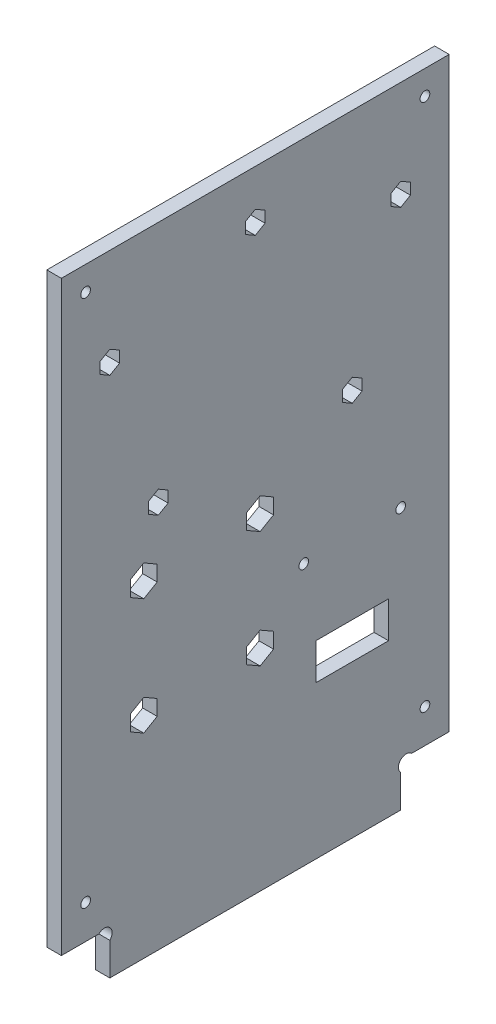
SolidWorks part; units mm, degrees
ref_plane "Plan de face" through (0, 0, 0) normal (0, 0, 1) x (1, 0, 0)
ref_plane "Plan de dessus" through (0, 0, 0) normal (0, 1, 0) x (1, 0, 0)
ref_plane "Plan de droite" through (0, 0, 0) normal (1, 0, 0) x (0, 0, -1)
sketch "Esquisse1" plane through (0, 0, 0) normal (1, 0, 0) x (0, 0, -1)
  line L8 (10, 6.7373) -> (10, 0)
  line L9 (70, 6.7373) -> (70, 0)
  line L10 (7.7373, 9) -> (0, 9)
  line L11 (10, 0) -> (70, 0)
  line L12 (72.2627, 9) -> (80, 9)
  line L13 (0, 9) -> (0, 130)
  line L14 (0, 130) -> (80, 130)
  line L15 (80, 130) -> (80, 9)
  arc A0 (10, 6.7373) -> (7.7373, 9) centre (8.8686, 7.8686) ccw
  arc A1 (70, 6.7373) -> (72.2627, 9) centre (71.1314, 7.8686) cw
  dimension "D7" = 1.1314
  dimension "D6" = 1.6
  dimension "D1" = 9
  dimension "D2" = 10
  dimension "D3" = 10
  dimension "D4" = 80
  dimension "D5" = 130
  dimension "D8" = 1.1314
  dimension "D9" = 1.1314
  dimension "D10" = 1.1314
extrude "Extrusion1" add sketch "Esquisse1" along normal blind 3
sketch "Esquisse2" plane through (3, 0, 0) normal (1, 0, 0) x (0, 0, -1)
  line L0 (0, 9) -> (7.7373, 9) construction
  line L1 (0, 130) -> (0, 9) construction
  line L2 (80, 9) -> (80, 130) construction
  line L3 (72.2627, 9) -> (80, 9) construction
  line L4 (80, 130) -> (0, 130) construction
  circle A0 centre (60, 80) radius 1
  circle A1 centre (10, 110) radius 1
  circle A2 centre (20, 80) radius 1
  circle A3 centre (70, 110) radius 1
  circle A4 centre (17, 67.45) radius 1.5
  circle A5 centre (17, 43.45) radius 1.5
  circle A6 centre (41, 43.45) radius 1.5
  circle A7 centre (41, 67.45) radius 1.5
  circle A8 centre (40, 120) radius 1
  circle A9 centre (70, 54) radius 1
  circle A10 centre (50, 54) radius 1
  dimension "D5" = 17
  dimension "D7" = 10
  dimension "D9" = 10
  dimension "D4" = 3
  dimension "D6" = 2
  dimension "D1" = 58.45
  dimension "D2" = 24
  dimension "D3" = 24
  dimension "D8" = 40
  dimension "D10" = 30
  dimension "D11" = 10
  dimension "D12" = 20
  dimension "D13" = 10
  dimension "D14" = 10
  dimension "D15" = 10
  dimension "D16" = 20
  dimension "D17" = 45
extrude "Enlèv. mat.-Extru.1" cut sketch "Esquisse2" against normal through all
sketch "Esquisse3" plane through (0, 0, 0) normal (-1, 0, 0) x (0, 0, 1)
  line L1 (-67.5, 39) -> (-52.5, 39)
  line L2 (-67.5, 39) -> (-67.5, 31.5)
  line L3 (-67.5, 31.5) -> (-52.5, 31.5)
  line L4 (-52.5, 39) -> (-52.5, 31.5)
  circle A0 centre (-70, 54) radius 1 construction
  circle A1 centre (-50, 54) radius 1 construction
  dimension "D4" = 2.5
  dimension "D1" = 15
  dimension "D2" = 7.5
  dimension "D3" = 15
  dimension "D5" = 2.5
extrude "Enlèv. mat.-Extru.2" cut sketch "Esquisse3" against normal through all
sketch "Esquisse4" plane through (3, 0, 0) normal (1, 0, 0) x (0, 0, -1)
  line L0 (80, 130) -> (0, 130) construction
  line L1 (0, 130) -> (0, 9) construction
  line L2 (80, 9) -> (80, 130) construction
  line L3 (0, 9) -> (7.7373, 9) construction
  circle A0 centre (5, 125) radius 1
  circle A1 centre (75, 125) radius 1
  circle A2 centre (75, 16) radius 1
  circle A3 centre (5, 16) radius 1
  dimension "D1" = 2
  dimension "D2" = 5
  dimension "D3" = 5
  dimension "D4" = 5
  dimension "D5" = 7
extrude "Enlèv. mat.-Extru.3" cut sketch "Esquisse4" against normal through all
sketch "Esquisse5" plane through (3, 0, 0) normal (1, 0, 0) x (0, 0, -1)
  line L0 (0, 130) -> (0, 9) construction
  line L1 (12.0178, 111.165) -> (10, 112.33)
  line L2 (10, 112.33) -> (7.9822, 111.165)
  line L3 (7.9822, 111.165) -> (7.9822, 108.835)
  line L4 (7.9822, 108.835) -> (10, 107.67)
  line L5 (10, 107.67) -> (12.0178, 108.835)
  line L6 (12.0178, 108.835) -> (12.0178, 111.165)
  line L7 (0, 130) -> (0, 9) construction
  line L26 (42.0178, 118.835) -> (42.0178, 121.165)
  line L27 (42.0178, 121.165) -> (40, 122.33)
  line L28 (40, 122.33) -> (37.9822, 121.165)
  line L29 (37.9822, 121.165) -> (37.9822, 118.835)
  line L30 (37.9822, 118.835) -> (40, 117.67)
  line L31 (40, 117.67) -> (42.0178, 118.835)
  line L32 (70, 107.67) -> (72.0178, 108.835)
  line L33 (72.0178, 108.835) -> (72.0178, 111.165)
  line L34 (72.0178, 111.165) -> (70, 112.33)
  line L35 (70, 112.33) -> (67.9822, 111.165)
  line L36 (67.9822, 111.165) -> (67.9822, 108.835)
  line L37 (67.9822, 108.835) -> (70, 107.67)
  line L38 (62.0178, 78.835) -> (62.0178, 81.165)
  line L39 (62.0178, 81.165) -> (60, 82.33)
  line L40 (60, 82.33) -> (57.9822, 81.165)
  line L41 (57.9822, 81.165) -> (57.9822, 78.835)
  line L42 (57.9822, 78.835) -> (60, 77.67)
  line L43 (60, 77.67) -> (62.0178, 78.835)
  line L44 (22.0178, 78.835) -> (22.0178, 81.165)
  line L45 (22.0178, 81.165) -> (20, 82.33)
  line L46 (20, 82.33) -> (17.9822, 81.165)
  line L47 (17.9822, 81.165) -> (17.9822, 78.835)
  line L48 (17.9822, 78.835) -> (20, 77.67)
  line L49 (20, 77.67) -> (22.0178, 78.835)
  line L56 (43.7713, 65.85) -> (43.7713, 69.05)
  line L57 (43.7713, 69.05) -> (41, 70.65)
  line L58 (41, 70.65) -> (38.2287, 69.05)
  line L59 (38.2287, 69.05) -> (38.2287, 65.85)
  line L60 (38.2287, 65.85) -> (41, 64.25)
  line L61 (41, 64.25) -> (43.7713, 65.85)
  line L62 (43.7713, 41.85) -> (43.7713, 45.05)
  line L63 (43.7713, 45.05) -> (41, 46.65)
  line L64 (41, 46.65) -> (38.2287, 45.05)
  line L65 (38.2287, 45.05) -> (38.2287, 41.85)
  line L66 (38.2287, 41.85) -> (41, 40.25)
  line L67 (41, 40.25) -> (43.7713, 41.85)
  line L68 (19.7713, 41.85) -> (19.7713, 45.05)
  line L69 (19.7713, 45.05) -> (17, 46.65)
  line L70 (17, 46.65) -> (14.2287, 45.05)
  line L71 (14.2287, 45.05) -> (14.2287, 41.85)
  line L72 (14.2287, 41.85) -> (17, 40.25)
  line L73 (17, 40.25) -> (19.7713, 41.85)
  line L75 (19.7713, 65.85) -> (19.7713, 69.05)
  line L76 (19.7713, 69.05) -> (17, 70.65)
  line L77 (17, 70.65) -> (14.2287, 69.05)
  line L78 (14.2287, 69.05) -> (14.2287, 65.85)
  line L79 (14.2287, 65.85) -> (17, 64.25)
  line L80 (17, 64.25) -> (19.7713, 65.85)
  circle A0 centre (10, 110) radius 2.0178 construction
  circle A1 centre (40, 120) radius 2.0178 construction
  circle A2 centre (70, 110) radius 2.0178 construction
  circle A3 centre (60, 80) radius 2.0178 construction
  circle A4 centre (20, 80) radius 2.0178 construction
  circle A5 centre (17, 67.45) radius 2.7713 construction
  circle A6 centre (41, 67.45) radius 2.7713 construction
  circle A7 centre (41, 43.45) radius 2.7713 construction
  circle A8 centre (17, 43.45) radius 2.7713 construction
  dimension "D1" = 2.33
  dimension "D2" = 2.33
  dimension "D3" = 2.33
  dimension "D4" = 2.33
  dimension "D5" = 2.33
  dimension "D6" = 3.2
  dimension "D7" = 3.2
  dimension "D8" = 3.2
  dimension "D9" = 3.2
extrude "Enlèv. mat.-Extru.4" cut sketch "Esquisse5" against normal through all
